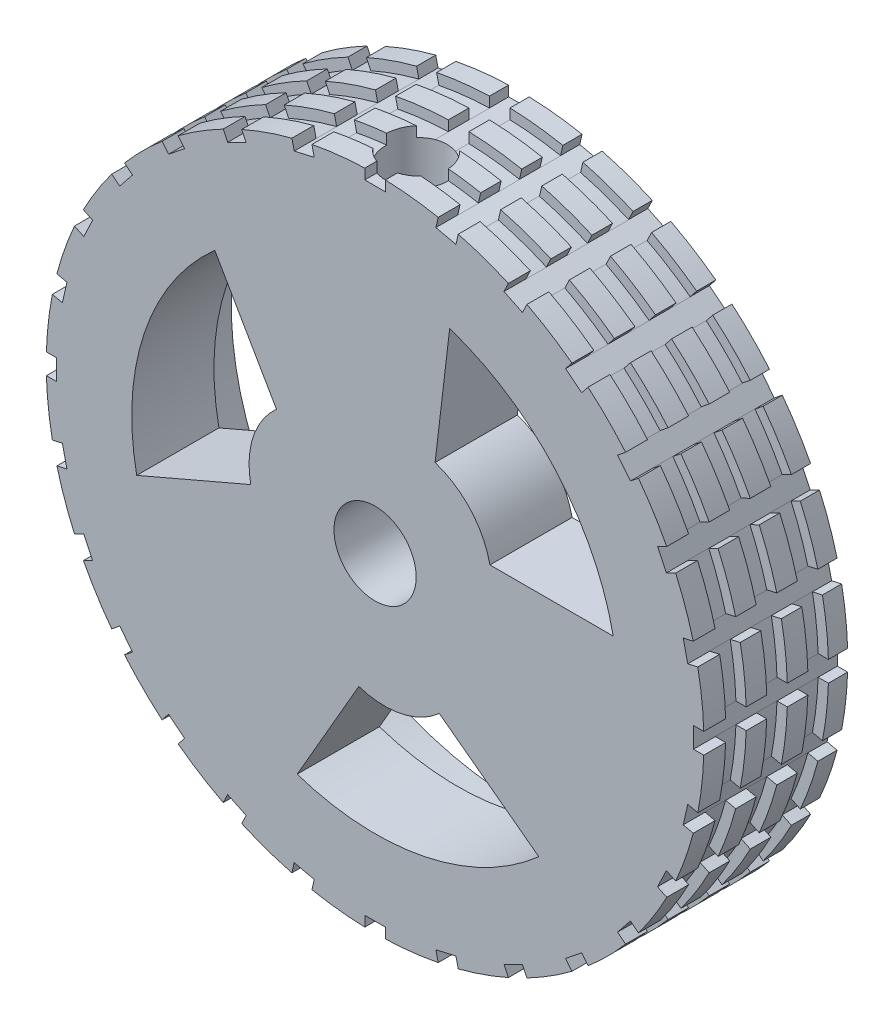
SolidWorks part; units mm, degrees
ref_plane "Front Plane" through (0, 0, 0) normal (0, 0, 1) x (1, 0, 0)
ref_plane "Top Plane" through (0, 0, 0) normal (0, 1, 0) x (1, 0, 0)
ref_plane "Right Plane" through (0, 0, 0) normal (1, 0, 0) x (0, 0, -1)
sketch "Sketch1" plane through (0, 0, 0) normal (1, 0, 0) x (0, 0, -1)
  line L0 (0, 0) -> (0, 16)
  line L1 (0, 16) -> (7, 16)
  line L2 (7, 16) -> (7, 14)
  line L3 (7, 14) -> (4, 14)
  line L4 (4, 14) -> (4, 4)
  line L5 (4, 4) -> (5, 4)
  line L6 (5, 4) -> (5, 2)
  line L7 (5, 2) -> (0, 2)
  line L8 (0, 0) -> (20.9231, 0) construction
  dimension "D1" = 4
  dimension "D2" = 7
  dimension "D3" = 4
  dimension "D4" = 5
  dimension "D5" = 16
  dimension "D6" = 2
  dimension "D7" = 14
revolve "Revolve1" add sketch "Sketch1" angle 360 about L8
sketch "Sketch3" plane through (0, 0, 0) normal (1, 0, 0) x (0, 0, -1)
  line L0 (2, 0) -> (2.9, 0)
  line L1 (2.9, 0) -> (2.9, 11.5)
  line L2 (2.9, 11.5) -> (3.5, 11.5)
  line L3 (3.5, 11.5) -> (3.5, 16)
  line L4 (3.5, 16) -> (2, 16)
  line L5 (2, 16) -> (2, 0)
  line L6 (7, 16) -> (0, 16) construction
  line L7 (2, 0) -> (2, 30.4989) construction
  dimension "D1" = 2
  dimension "D2" = 4.5
  dimension "D3" = 3
  dimension "D4" = 1.8
revolve "Cut-Revolve1" cut sketch "Sketch3" angle 360 about L7
sketch "Sketch6" plane through (0, 0, 0) normal (1, 0, 0) x (0, 0, -1)
  line L0 (7, 16) -> (3.5, 16) construction
  line L1 (5.0656, 16) -> (6.0656, 16)
  line L2 (5.0656, 16) -> (5.0656, 15.5)
  line L3 (5.0656, 15.5) -> (6.0656, 15.5)
  line L4 (6.0656, 16) -> (6.0656, 15.5)
  line L5 (7, -16) -> (7, 16) construction
  line L6 (0, 0) -> (7, 0) construction
  dimension "D1" = 0.5
  dimension "D2" = 1
revolve "Cut-Revolve2" cut sketch "Sketch6" angle 360 about L6
sketch "Sketch7" plane through (0, 0, -7) normal (0, 0, -1) x (-1, 0, 0)
  line L0 (0, 0) -> (0, 19.1495) construction
  line L2 (-0.5, 15.9922) -> (-0.5, 15.4922)
  line L3 (-0.5, 15.4922) -> (0.5, 15.4922)
  line L4 (0.5, 15.9922) -> (0.5, 15.4922)
  circle A0 centre (0, 0) radius 16 construction
  arc A1 (0.5, 15.9922) -> (-0.5, 15.9922) centre (0, 0) ccw
  dimension "D1" = 0.5
  dimension "D2" = 0.5
  dimension "D3" = 0.5
extrude "Cut-Extrude3" cut sketch "Sketch7" against normal blind 10
pattern_circular "CirPattern3" count 28 over 360 about axis through (0, 0, 0) along (0, 0, 1) of "Cut-Extrude3"
pattern_linear "LPattern1" count 3 spacing 2 along (0, 0, 1) of "Cut-Revolve2"
sketch "Sketch9" plane through (0, 0, -4) normal (0, 0, -1) x (-1, 0, 0)
  line L2 (0, 0) -> (0, 18.4059) construction
  line L7 (-11.5877, 2.3145) -> (-5.5877, 2.3145)
  line L9 (-2.9211, 5.296) -> (-3.6293, 11.296)
  line L11 (0, 0) -> (-15.4092, 13.7824) construction
  arc A6 (-5.5877, 2.3145) -> (-2.9211, 5.296) centre (-1.6724, 1.4958) cw
  arc A7 (-11.5877, 2.3145) -> (-3.6293, 11.296) centre (0.1695, -0.0869) cw
  dimension "D7" = 4
  dimension "D8" = 12
  dimension "D9" = 4
  dimension "D1" = 6
  dimension "D2" = 6
  dimension "D3" = 2
  dimension "D4" = 2
  dimension "D5" = 6
  dimension "D6" = 6
extrude "Cut-Extrude6" cut sketch "Sketch9" against normal blind 10 contours A7 L9 A6 L7
pattern_circular "CirPattern8" count 3 over 360 about axis through (0, 0, 0) along (0, 0, 1) of "Cut-Extrude6"
